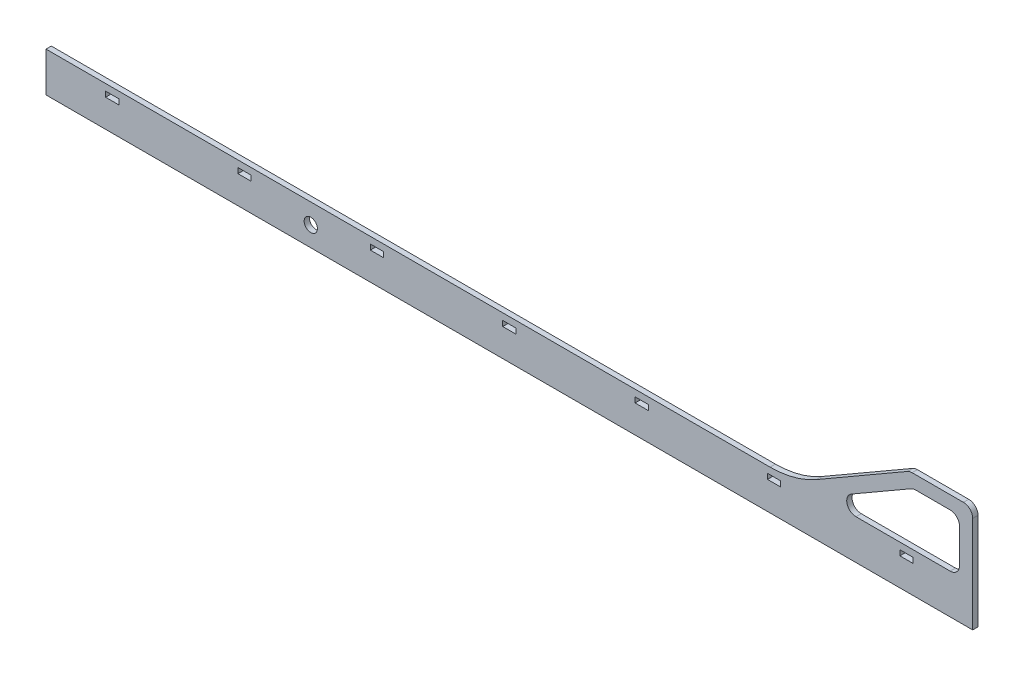
SolidWorks part; units mm, degrees
ref_plane "Piano frontale" through (0, 0, 0) normal (0, 0, 1) x (1, 0, 0)
ref_plane "Piano superiore" through (0, 0, 0) normal (0, 1, 0) x (1, 0, 0)
ref_plane "Piano destro" through (0, 0, 0) normal (1, 0, 0) x (0, 0, -1)
sketch "Schizzo1" plane through (0, 0, 0) normal (0, 0, 1) x (1, 0, 0)
  line L0 (145, 25) -> (155, 25)
  line L1 (0, 0) -> (700, 0)
  line L2 (0, 0) -> (0, 30)
  line L3 (0, 30) -> (546.9591, 30)
  line L4 (700, 0) -> (700, 30)
  line L5 (45, 25) -> (55, 25)
  line L6 (45, 25) -> (45, 21)
  line L7 (45, 21) -> (55, 21)
  line L8 (55, 25) -> (55, 21)
  line L9 (145, 25) -> (145, 21)
  line L10 (145, 21) -> (155, 21)
  line L11 (155, 25) -> (155, 21)
  line L12 (245, 25) -> (255, 25)
  line L13 (245, 25) -> (245, 21)
  line L14 (245, 21) -> (255, 21)
  line L15 (255, 25) -> (255, 21)
  line L16 (345, 25) -> (355, 25)
  line L17 (345, 25) -> (345, 21)
  line L18 (345, 21) -> (355, 21)
  line L19 (355, 25) -> (355, 21)
  line L20 (445, 25) -> (455, 25)
  line L21 (445, 25) -> (445, 21)
  line L22 (445, 21) -> (455, 21)
  line L23 (455, 25) -> (455, 21)
  line L24 (545, 25) -> (555, 25)
  line L25 (545, 25) -> (545, 21)
  line L26 (545, 21) -> (555, 21)
  line L27 (555, 25) -> (555, 21)
  line L28 (645, 25) -> (655, 25)
  line L29 (645, 25) -> (645, 21)
  line L30 (645, 21) -> (655, 21)
  line L31 (655, 25) -> (655, 21)
  line L32 (654.1937, 80) -> (693, 80)
  line L34 (700, 73) -> (700, 30)
  line L35 (650.6937, 79.0622) -> (581.9591, 39.3782)
  line L36 (690, 63) -> (690, 37)
  line L37 (656.8732, 70) -> (683, 70)
  line L38 (653.3732, 69.0622) -> (608.3399, 43.0622)
  line L39 (611.8399, 30) -> (683, 30)
  line L40 (654.9976, 70) -> (570.7156, 21.3397) construction
  line L41 (654.9976, 70) -> (690, 70) construction
  line L42 (690, 70) -> (690, 30) construction
  line L43 (652.3181, 80) -> (700, 80) construction
  line L44 (700, 80) -> (700, 30) construction
  line L45 (652.3181, 80) -> (565.7156, 30) construction
  arc A0 (611.8399, 30) -> (608.3399, 43.0622) centre (611.8399, 37) cw
  arc A1 (656.8732, 70) -> (653.3732, 69.0622) centre (656.8732, 63) ccw
  arc A2 (683, 30) -> (690, 37) centre (683, 37) ccw
  arc A3 (690, 63) -> (683, 70) centre (683, 63) ccw
  arc A4 (693, 80) -> (700, 73) centre (693, 73) cw
  arc A5 (654.1937, 80) -> (650.6937, 79.0622) centre (654.1937, 73) ccw
  arc A6 (581.9591, 39.3782) -> (546.9591, 30) centre (546.9591, 100) cw
  circle A7 centre (200, 15) radius 5
  dimension "D11" = 30
  dimension "D13" = 7
  dimension "D14" = 70
  dimension "D10" = 65
  dimension "D12" = 10
  dimension "D15" = 153.0409
  dimension "D16" = 43
  dimension "D21" = 10
  dimension "D17" = 26
  dimension "D1" = 30
  dimension "D2" = 700
  dimension "D3" = 10
  dimension "D4" = 4
  dimension "D5" = 5
  dimension "D6" = 45
  dimension "D8" = 21
  dimension "D9" = 45
  dimension "D22" = 15
  dimension "D23" = 45
  dimension "D7" = 7
extrude "Estrusione-Estrusione3" add sketch "Schizzo1" along normal blind 4
